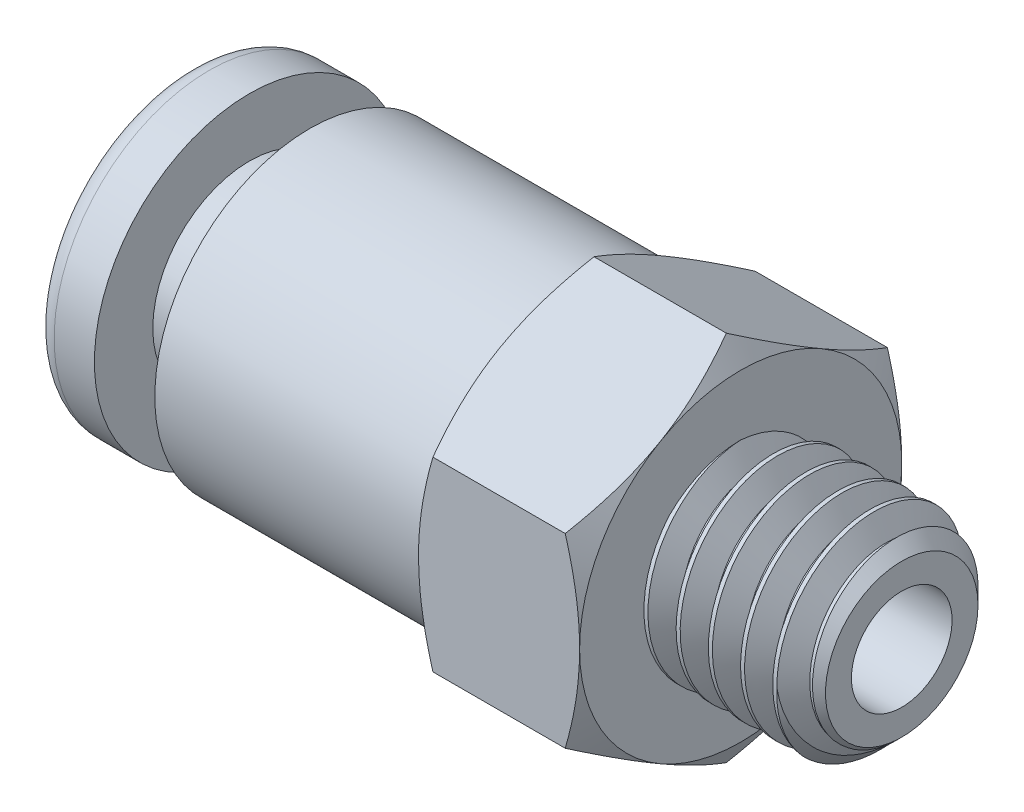
SolidWorks part; units mm, degrees
ref_plane "Front Plane" through (0, 0, 0) normal (0, 0, 1) x (1, 0, 0)
ref_plane "Top Plane" through (0, 0, 0) normal (0, 1, 0) x (1, 0, 0)
ref_plane "Right Plane" through (0, 0, 0) normal (1, 0, 0) x (0, 0, -1)
sketch "Sketch0" plane through (0, 0, 0) normal (0, 0, -1) x (-1, 0, 0)
  line L0 (0, 0) -> (-17.7, 0) construction
  line L1 (0, 3.85) -> (0, -3.85) construction
  line L2 (-13.3, 2) -> (-13.3, -2) construction
  line L3 (-13.7, 2.5) -> (-13.7, -2.5) construction
  line L4 (-8.85, 4) -> (-8.85, -4) construction
  line L5 (-17.7, 1.25) -> (-17.7, -1.25) construction
  point P3 (-13.3, 0)
  point P11 (-8.85, 0)
  point P16 (-14.7, 0)
  point P17 (-13.7, 0)
  dimension "L" = 17.7
  dimension "M" = 13.3
  dimension "A" = 14.7
  dimension "D" = 7.7
  dimension "Tube OD" = 4
  dimension "Thread OD" = 5
  dimension "H" = 8
  dimension "ID" = 2.5
  dimension "Thread Length" = 4
sketch "Sketch1" plane through (0, 0, 0) normal (0, 0, -1) x (-1, 0, 0)
  line L0 (0, 3.35) -> (0, 2.5)
  line L1 (-0.5, 3.85) -> (-1.5, 3.85)
  line L2 (-1.5, 3.85) -> (-1.5, 2.4)
  line L3 (-1.5, 2.4) -> (-3, 2.4)
  line L4 (-3, 2.4) -> (-3, 3.85)
  line L5 (-3, 3.85) -> (-13.7, 3.85)
  line L6 (-13.7, 3.85) -> (-13.7, 0)
  line L7 (0, 0) -> (-17.7, 0) construction
  line L8 (-13.7, 0) -> (-13.3, 0)
  line L9 (-13.3, 2) -> (-13.3, 0)
  line L10 (0, 0) -> (-17.7, 0) construction
  line L11 (-13.3, 2) -> (-0.5, 2)
  line L12 (0, 3.85) -> (0, -3.85) construction
  line L13 (0, 2.5) -> (-0.5, 2)
  line L14 (-13.7, 2.5) -> (-13.7, -2.5) construction
  arc A0 (0, 3.35) -> (-0.5, 3.85) centre (-0.5, 3.35) ccw
  arc A1 (-0.5, 2) -> (0, 2.5) centre (-0.5, 2.5) ccw construction
  point P15 (0, 3.85)
  point P19 (0, 3.85)
  point P25 (0, 2)
  dimension "R" = 0.5
  dimension "D1" = 1.5
  dimension "D3" = 4.8
  dimension "D2" = 1.5
revolve "Revolve2" add sketch "Sketch1" angle 360 about L10
ref_plane "Plane1" through (13.7, 0, 0) normal (1, 0, 0) x (0, 0, -1)
sketch "Sketch2" plane through (13.7, 0, 0) normal (1, 0, 0) x (0, 0, -1)
  circle A0 centre (0, 0) radius 2.5
  point P5 (0, -2.5)
extrude "Extrude1" add sketch "Sketch2" along normal up to vertex (4 mm away) separate body up to point (17.7, 0, 0)
sketch "Sketch3" plane through (17.7, 0, 0) normal (1, 0, 0) x (0, 0, -1)
  circle A1 centre (0, 0) radius 2.5
  circle A2 centre (0, 0) radius 2.5
  point P0 (0, 2.5)
  dimension "D1" = 0
curve "Helix/Spiral1" pitch 0.8 height 6.8 turns 8.5 parameters "Height"=6.8, "Pitch"=0.8
sketch "Sketch4" plane through (0, 0, 0) normal (0, 0, -1) x (-1, 0, 0)
  line L0 (-18.45, 2.5866) -> (-18.05, 1.8938) construction
  line L1 (-18.05, 1.8938) -> (-17.65, 2.5866) construction
  line L2 (-17.65, 2.5866) -> (-18.45, 2.5866) construction
  line L3 (-18.4, 2.5) -> (-17.7, 2.5) construction
  line L4 (-18.05, 2.5866) -> (-18.05, 2.5) construction
  line L5 (-18.05, 2.5) -> (-18.05, 1.9804) construction
  line L6 (-18.05, 1.9804) -> (-18.05, 1.8938) construction
  line L7 (-18.1, 1.9804) -> (-18, 1.9804)
  line L8 (-17.65, 2.5866) -> (-18.4, 2.5)
  line L9 (-17.65, 2.5866) -> (-18, 1.9804)
  line L10 (-18.4, 2.5) -> (-18.1, 1.9804)
  line L11 (-18.05, 1.8938) -> (-18.05, -2.5) construction
  line L12 (-18.05, -2.5) -> (-17.25, -2.5) construction
  line L13 (-17.25, -2.5) -> (-16.45, -2.5) construction
  line L14 (-16.45, -2.5) -> (-15.65, -2.5) construction
  line L15 (-15.65, -2.5) -> (-14.85, -2.5) construction
  line L16 (-17.7, -2.5) -> (-13.7, -2.5) construction
  dimension "D1" = 0.8
  dimension "D2" = 0.1
sketch "Sketch5" plane through (17.7, 0, 0) normal (1, 0, 0) x (0, 0, -1)
  circle A0 centre (0, 0) radius 1.8938
extrude "Extrude2" cut sketch "Sketch5" against normal up to vertex (3 mm away) draft 45 flip side to cut up to point (14.7, 0, 0)
sweep "Cut-Sweep1" cut profiles "Sketch4" path "Helix/Spiral1"
sketch "Sketch7" plane through (17.7, 0, 0) normal (1, 0, 0) x (0, 0, -1)
  circle A0 centre (0, 0) radius 1.25
extrude "Extrude4" cut sketch "Sketch7" against normal up to vertex (17.7 mm away) up to point (0, 0, 0)
sketch "Sketch8" plane through (13.7, 0, 0) normal (1, 0, 0) x (0, 0, -1)
  line L1 (0, 4.6188) -> (-4, 2.3094)
  line L2 (-4, 2.3094) -> (-4, -2.3094)
  line L3 (-4, -2.3094) -> (0, -4.6188)
  line L4 (0, -4.6188) -> (4, -2.3094)
  line L5 (4, -2.3094) -> (4, 2.3094)
  line L6 (4, 2.3094) -> (0, 4.6188)
  circle A0 centre (0, 0) radius 4 construction
  circle A1 centre (0, 0) radius 3.85 construction
  circle A3 centre (0, 0) radius 3.85
extrude "Extrude5" add sketch "Sketch8" against normal blind 4
sketch "Sketch9" plane through (13.7, 0, 0) normal (1, 0, 0) x (0, 0, -1)
  circle A0 centre (0, 0) radius 4 construction
  circle A1 centre (0, 0) radius 4
extrude "Extrude6" cut sketch "Sketch9" against normal up to vertex (4 mm away) draft 60 flip side to cut up to point (9.7, 4.6188, 0)
sketch "Sketch10" plane through (9.7, 0, 0) normal (-1, 0, 0) x (0, 0, 1)
  circle A1 centre (0, 0) radius 4
  circle A2 centre (0, 0) radius 4
  dimension "D1" = 0
extrude "Extrude7" cut sketch "Sketch10" against normal up to vertex (4 mm away) draft 60 flip side to cut up to point (13.7, 4.6188, 0)
combine bodies "Combine1" operation type add bodies to combine 116 109
equation "\"Height@Helix/Spiral1\" = \"Pitch@Helix/Spiral1\" +  ( \"Thread Length@Sketch0\" * 1.5 ) "
equation "\"D1@Sketch4\" = \"Pitch@Helix/Spiral1\""
equation "\"D2@Sketch4\" = \"D1@Sketch4\" * 1 / 8"
